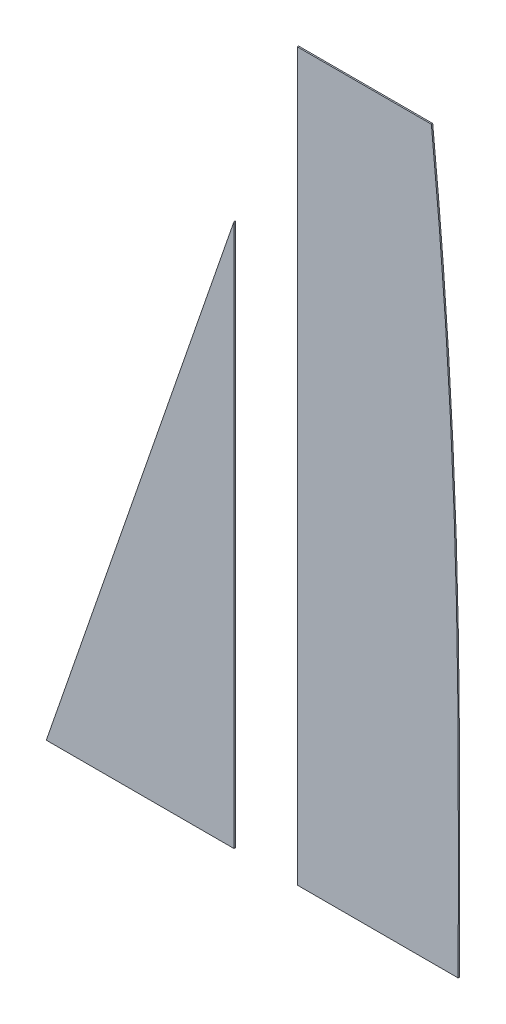
SolidWorks part; units mm, degrees
ref_plane "Front Plane" through (0, 0, 0) normal (0, 0, 1) x (1, 0, 0)
ref_plane "Top Plane" through (0, 0, 0) normal (0, 1, 0) x (1, 0, 0)
ref_plane "Right Plane" through (0, 0, 0) normal (1, 0, 0) x (0, 0, -1)
sketch "Sketch1" plane through (0, 0, 0) normal (0, 0, 1) x (1, 0, 0)
  line L0 (0, 0) -> (0, 1028.7)
  line L1 (0, 1028.7) -> (-355.6, 0)
  line L2 (-355.6, 0) -> (0, 0)
  line L3 (373.7515, 1375.124) -> (119.7515, 1375.124)
  line L4 (119.7515, 1375.124) -> (119.7515, 0)
  line L5 (119.7515, 0) -> (424.5515, 0)
  line L6 (0, 1028.7) -> (119.7515, 1375.124) construction
  spline S0 degree 3 poles (424.5515, 0) (424.5729, 401.7772) (432.3047, 795.4353) (373.7515, 1375.124) knots 0 0 0 0 1 1 1 1
  dimension "D1" = 1028.7
  dimension "D2" = 1375.124
  dimension "D3" = 304.8
  dimension "D4" = 254
  dimension "D5" = 355.6
extrude "Boss-Extrude1" add sketch "Sketch1" along normal blind 2.54
